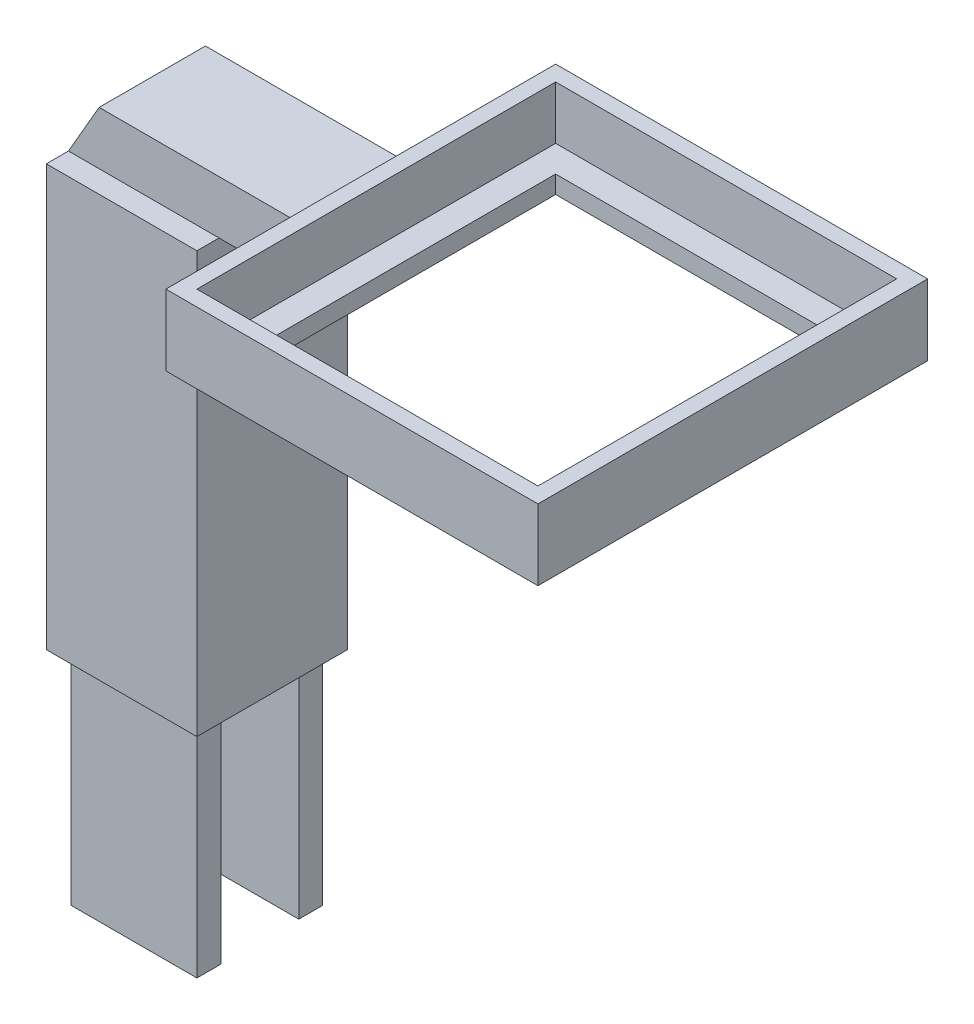
SolidWorks part; units mm, degrees
ref_plane "Front Plane" through (0, 0, 0) normal (0, 0, 1) x (1, 0, 0)
ref_plane "Top Plane" through (0, 0, 0) normal (0, 1, 0) x (1, 0, 0)
ref_plane "Right Plane" through (0, 0, 0) normal (1, 0, 0) x (0, 0, -1)
sketch "Sketch1" plane through (0, 0, 0) normal (0, 1, 0) x (1, 0, 0)
  line L1 (8.5, -8.5) -> (-8.5, -8.5)
  line L2 (8.5, -8.5) -> (8.5, 8.5)
  line L3 (8.5, 8.5) -> (-8.5, 8.5)
  line L4 (-8.5, -8.5) -> (-8.5, 8.5)
  line L5 (8.5, -8.5) -> (7.5, -7.5) construction
  line L6 (8.5, 8.5) -> (-7.1, -7.1) construction
  line L11 (7.1, -7.1) -> (-7.5, 7.5) construction
  line L12 (7.5, 7.5) -> (-7.1, -7.1) construction
  line L17 (7.5, -4) -> (-7.5, 4) construction
  line L18 (7.5, 4) -> (-7.5, -4) construction
  line L20 (7.1, -7.1) -> (-7.1, -7.1)
  line L21 (-7.1, -7.1) -> (-7.1, -4.4)
  line L22 (7.1, -4.4) -> (-7.1, -4.4)
  line L23 (7.1, -7.1) -> (7.1, -4.4)
  line L24 (7.1, 7.1) -> (-7.1, 7.1)
  line L25 (-7.1, 4.4) -> (-7.1, 7.1)
  line L26 (7.1, 4.4) -> (-7.1, 4.4)
  line L27 (7.1, 4.4) -> (7.1, 7.1)
  line L29 (-7.5, -7.5) -> (-8.5, -8.5) construction
  line L31 (7.1, -7.1) -> (-8.5, 8.5) construction
  point P0 (0, 0)
  point P6 (0, 0)
  point P11 (0, 0)
  dimension "D1" = 17
  dimension "D2" = 17
  dimension "D3" = 15
  dimension "D4" = 15
extrude "Boss-Extrude1" add sketch "Sketch1" along normal blind 25 contours L20 L23 L22 L21 | L26 L27 L24 L25
sketch "Sketch2" plane through (0, 25, 0) normal (0, 1, 0) x (1, 0, 0)
  line L1 (8.5, -8.5) -> (-8.5, -8.5)
  line L2 (8.5, -8.5) -> (8.5, 8.5)
  line L3 (8.5, 8.5) -> (-8.5, 8.5)
  line L4 (-8.5, -8.5) -> (-8.5, 8.5)
  line L5 (8.5, -8.5) -> (-8.5, 8.5) construction
  line L6 (8.5, 8.5) -> (-8.5, -8.5) construction
  point P0 (0, 0)
  dimension "D1" = 17
  dimension "D2" = 17
extrude "Boss-Extrude2" add sketch "Sketch2" along normal blind 47.5
ref_plane "Plane1" through (0, 0, 0) normal (0, 0, 1) x (1, 0, 0)
sketch "Sketch5" plane through (0, 0, 0) normal (0, 0, 1) x (1, 0, 0)
  line L0 (-8.5, 72.5) -> (-5.0359, 78.5)
  line L1 (-5.0359, 78.5) -> (18.5, 78.5)
  line L2 (18.5, 78.5) -> (18.5, 72.5)
  line L3 (18.5, 72.5) -> (-8.5, 72.5)
  line L4 (8.5, 72.5) -> (8.5, 25) construction
  dimension "D1" = 60
  dimension "D2" = 10
  dimension "D3" = 6
extrude "Boss-Extrude4" add sketch "Sketch5" along normal mid plane 12 contours L0 L1 L2 L3
sketch "Sketch6" plane through (0, 78.5, 0) normal (0, 1, 0) x (1, 0, 0)
  line L0 (18.5, -6) -> (18.5, 6) construction
  line L1 (60.5, -22) -> (18.5, -22)
  line L2 (60.5, -22) -> (60.5, 22)
  line L3 (60.5, 22) -> (18.5, 22)
  line L4 (18.5, -22) -> (18.5, 22)
  line L5 (60.5, -22) -> (18.5, 22) construction
  line L6 (60.5, 22) -> (18.5, -22) construction
  line L8 (58.75, -20.25) -> (20.25, -20.25)
  line L9 (58.75, -20.25) -> (58.75, 20.25)
  line L10 (58.75, 20.25) -> (20.25, 20.25)
  line L11 (20.25, -20.25) -> (20.25, 20.25)
  line L12 (58.75, -20.25) -> (20.25, 20.25) construction
  line L13 (58.75, 20.25) -> (20.25, -20.25) construction
  point P0 (39.5, 0)
  point P7 (18.5, 0)
  point P8 (39.5, 0)
  dimension "D1" = 42
  dimension "D2" = 44
  dimension "D3" = 40.5
  dimension "D4" = 38.5
extrude "Boss-Extrude5" add sketch "Sketch6" against normal blind 6 and the other way blind 2 from offset 0
sketch "Sketch7" plane through (0, 72.5, 0) normal (0, -1, 0) x (1, 0, 0)
  line L0 (20.25, 20.25) -> (58.75, -20.25) construction
  line L1 (20.25, 20.25) -> (58.75, 20.25)
  line L2 (20.25, 20.25) -> (20.25, -20.25)
  line L3 (20.25, -20.25) -> (58.75, -20.25)
  line L4 (58.75, 20.25) -> (58.75, -20.25)
  line L5 (58.75, 20.25) -> (20.25, -20.25) construction
  line L7 (55.75, -17.25) -> (23.25, -17.25)
  line L8 (55.75, -17.25) -> (55.75, 17.25)
  line L9 (55.75, 17.25) -> (23.25, 17.25)
  line L10 (23.25, -17.25) -> (23.25, 17.25)
  line L11 (55.75, -17.25) -> (23.25, 17.25) construction
  line L12 (55.75, 17.25) -> (23.25, -17.25) construction
  point P6 (39.5, 0)
  dimension "D1" = 34.5
  dimension "D2" = 32.5
extrude "Boss-Extrude6" add sketch "Sketch7" against normal blind 2
sketch "Sketch8" plane through (0, 0, 0) normal (0, 0, 1) x (1, 0, 0)
  line L0 (16, 72.5) -> (8.5, 59.5096)
  line L1 (18.5, 72.5) -> (8.5, 72.5) construction
  line L2 (8.5, 59.5096) -> (8.5, 72.5)
  line L3 (8.5, 72.5) -> (16, 72.5)
  dimension "D1" = 60
  dimension "D2" = 7.5
extrude "Boss-Extrude7" add sketch "Sketch8" along normal mid plane 6.5
